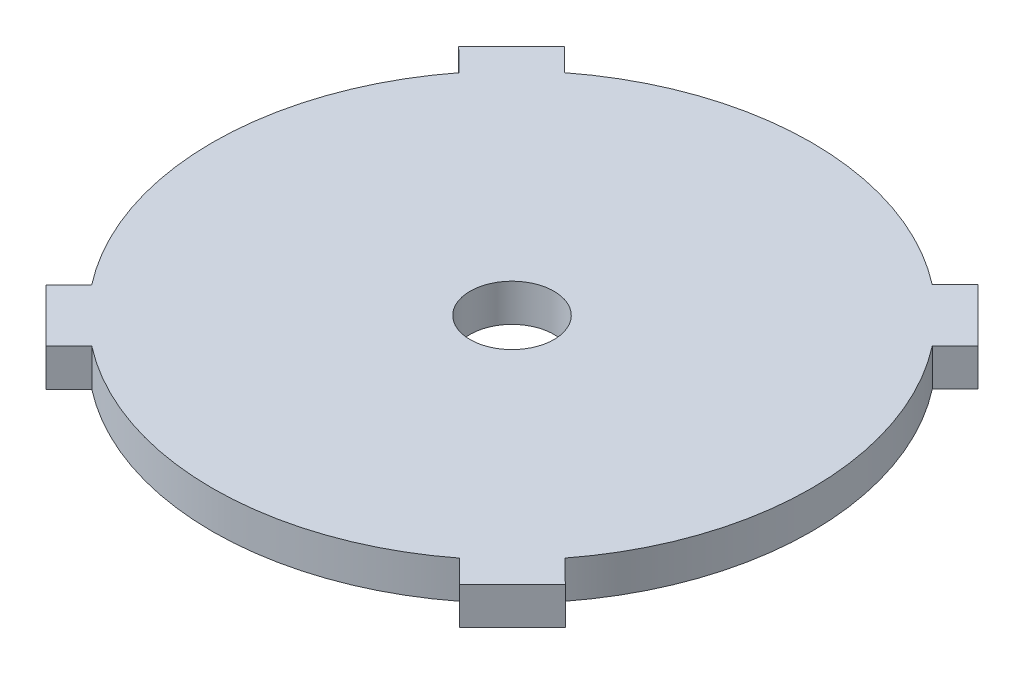
SolidWorks part; units mm, degrees
ref_plane "Front Plane" through (0, 0, 0) normal (0, 0, 1) x (1, 0, 0)
ref_plane "Top Plane" through (0, 0, 0) normal (0, 1, 0) x (1, 0, 0)
ref_plane "Right Plane" through (0, 0, 0) normal (1, 0, 0) x (0, 0, -1)
sketch "Sketch1" plane through (0, 0, 0) normal (0, 1, 0) x (1, 0, 0)
  line L14 (17.5258, -21.9902) -> (15.5876, -20.0546)
  line L15 (17.5258, -21.9902) -> (22.013, -17.4972)
  line L16 (-22.013, 17.4972) -> (-17.5258, 21.9902)
  line L17 (22.013, -17.4972) -> (20.0748, -15.5615)
  line L20 (-21.9902, -17.5258) -> (-20.0546, -15.5876)
  line L21 (-21.9902, -17.5258) -> (-17.4972, -22.013)
  line L22 (-17.4972, -22.013) -> (-15.5615, -20.0748)
  line L23 (17.4972, 22.013) -> (21.9902, 17.5258)
  line L24 (15.5615, 20.0748) -> (17.4972, 22.013)
  line L25 (20.0546, 15.5876) -> (21.9902, 17.5258)
  line L26 (-20.0748, 15.5615) -> (-22.013, 17.4972)
  line L27 (-15.5876, 20.0546) -> (-17.5258, 21.9902)
  arc A0 (15.5615, 20.0748) -> (-15.5876, 20.0546) centre (0, 0) ccw
  arc A13 (-20.0748, 15.5615) -> (-20.0546, -15.5876) centre (0, 0) ccw
  arc A14 (-15.5615, -20.0748) -> (15.5876, -20.0546) centre (0, 0) ccw
  arc A15 (20.0748, -15.5615) -> (20.0546, 15.5876) centre (0, 0) ccw
  circle A16 centre (0, 0) radius 3.556
  point P38 (0, 0)
  point P46 (0, 0)
  dimension "D1" = 6.35
  dimension "D5" = 50.8
  dimension "D2" = 7.112
  dimension "D9" = 27.94
  dimension "D10" = 2
extrude "Boss-Extrude1" add sketch "Sketch1" along normal blind 3.175
